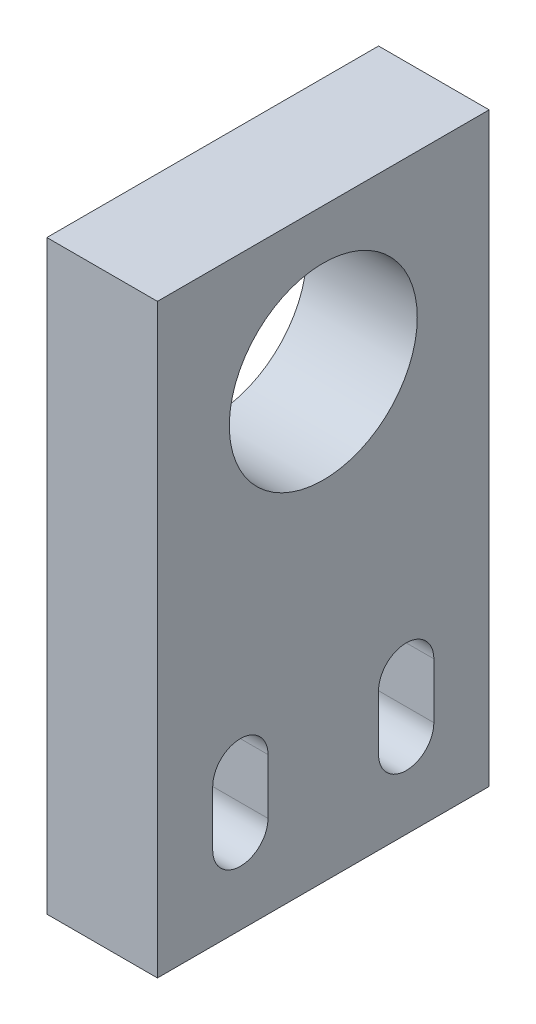
SolidWorks part; units mm, degrees
ref_plane "Front Plane" through (0, 0, 0) normal (0, 0, 1) x (1, 0, 0)
ref_plane "Top Plane" through (0, 0, 0) normal (0, 1, 0) x (1, 0, 0)
ref_plane "Right Plane" through (0, 0, 0) normal (1, 0, 0) x (0, 0, -1)
sketch "Sketch1" plane through (0, 0, 0) normal (1, 0, 0) x (0, 0, -1)
  line L0 (-15, 13) -> (15, 13)
  line L1 (15, 13) -> (15, -40)
  line L2 (15, -40) -> (-15, -40)
  line L3 (-15, -40) -> (-15, 13)
  line L4 (0, 13) -> (0, -40) construction
  line L5 (-7.5, -27.5) -> (-7.5, -32.5) construction
  line L6 (-5, -27.5) -> (-5, -32.5)
  line L7 (-10, -27.5) -> (-10, -32.5)
  line L8 (7.5, -27.5) -> (7.5, -32.5) construction
  line L9 (5, -27.5) -> (5, -32.5)
  line L10 (10, -27.5) -> (10, -32.5)
  circle A0 centre (0, 0) radius 8.5
  arc A2 (-5, -27.5) -> (-10, -27.5) centre (-7.5, -27.5) ccw
  arc A3 (-10, -32.5) -> (-5, -32.5) centre (-7.5, -32.5) ccw
  arc A4 (5, -27.5) -> (10, -27.5) centre (7.5, -27.5) cw
  arc A5 (10, -32.5) -> (5, -32.5) centre (7.5, -32.5) cw
  point P5 (0, 13)
  point P12 (-7.5, -30)
  point P17 (-7.5, -25)
  point P18 (-7.5, -35)
  point P21 (7.5, -30)
  dimension "D1" = 17
  dimension "D3" = 5
  dimension "D2" = 30
  dimension "D4" = 10
  dimension "D5" = 15
  dimension "D6" = 30
  dimension "D7" = 13
  dimension "D8" = 10
extrude "Boss-Extrude1" add sketch "Sketch1" along normal blind 10
